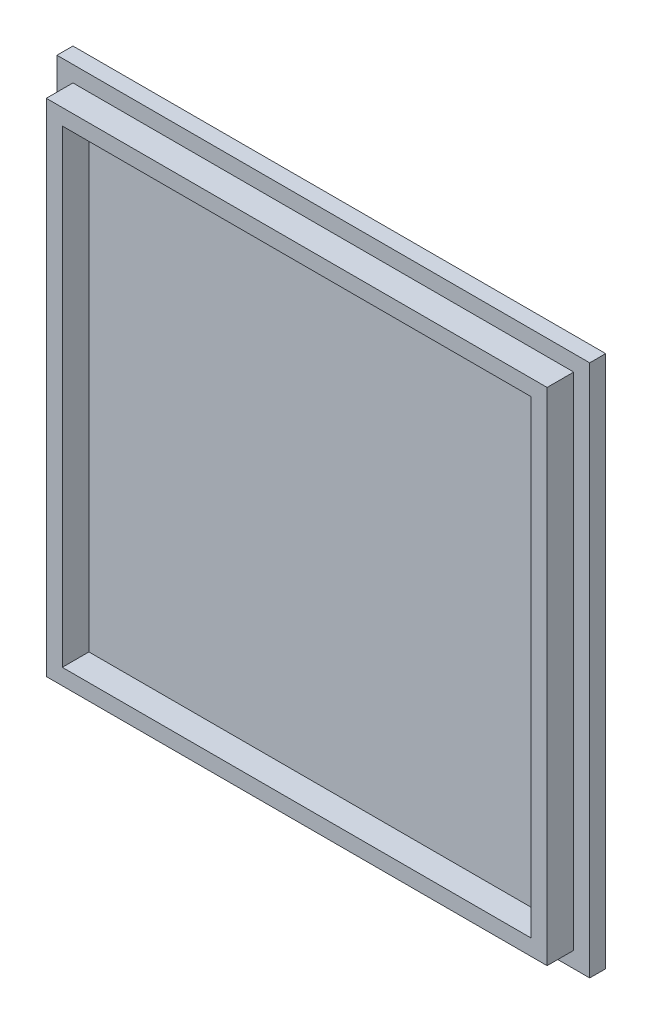
SolidWorks part; units mm, degrees
material "PVC 0.007 塑化"
ref_plane "前视基准面" through (0, 0, 0) normal (0, 0, 1) x (1, 0, 0)
ref_plane "上视基准面" through (0, 0, 0) normal (0, 1, 0) x (1, 0, 0)
ref_plane "右视基准面" through (0, 0, 0) normal (1, 0, 0) x (0, 0, -1)
sketch "草图1" plane through (0, 0, 0) normal (0, 0, 1) x (1, 0, 0)
  line L0 (-102.3873, 0) -> (86.4721, 0) construction
  line L1 (0, 98.1432) -> (0, -88.5942) construction
  line L2 (-48.5411, 52.5199) -> (51.4589, 52.5199)
  line L3 (51.4589, 52.5199) -> (51.4589, -47.4801)
  line L4 (51.4589, -47.4801) -> (-48.5411, -47.4801)
  line L5 (-48.5411, -47.4801) -> (-48.5411, 52.5199)
  dimension "D1" = 100
  dimension "D2" = 100
extrude "凸台-拉伸3" add sketch "草图1" along normal blind 8
sketch "草图4" plane through (0, 0, 8) normal (0, 0, 1) x (1, 0, 0)
  line L0 (-48.5411, 52.5199) -> (51.4589, 52.5199)
  line L1 (51.4589, 52.5199) -> (51.4589, -47.4801)
  line L2 (51.4589, -47.4801) -> (-48.5411, -47.4801)
  line L3 (-48.5411, -47.4801) -> (-48.5411, 52.5199)
  line L10 (45.4589, 46.5199) -> (-42.5411, 46.5199)
  line L11 (-42.5411, 46.5199) -> (-42.5411, -41.4801)
  line L12 (-42.5411, -41.4801) -> (45.4589, -41.4801)
  line L13 (45.4589, -41.4801) -> (45.4589, 46.5199)
  line L14 (-45.5411, -44.4801) -> (48.4589, -44.4801)
  line L15 (48.4589, -44.4801) -> (48.4589, 49.5199)
  line L16 (-45.5411, 49.5199) -> (-45.5411, -44.4801)
  line L17 (48.4589, 49.5199) -> (-45.5411, 49.5199)
  line L18 (-45.5411, -44.4801) -> (48.4589, -44.4801)
  line L19 (48.4589, -44.4801) -> (48.4589, 49.5199)
  line L20 (-45.5411, 49.5199) -> (-45.5411, -44.4801)
  line L21 (48.4589, 49.5199) -> (-45.5411, 49.5199)
  line M9 (-48.5411, 52.5199) -> (-48.5411, -47.4801)
  line M10 (-48.5411, -47.4801) -> (51.4589, -47.4801)
  line M11 (51.4589, -47.4801) -> (51.4589, 52.5199)
  line M12 (51.4589, 52.5199) -> (-48.5411, 52.5199)
  dimension "D1" = 3
  dimension "D2" = 3
extrude "切除-拉伸3" cut sketch "草图4" against normal blind 5 contours L21 L19 L18 L20 M12 M9 M10 M11 | L12 L13 L10 L11
